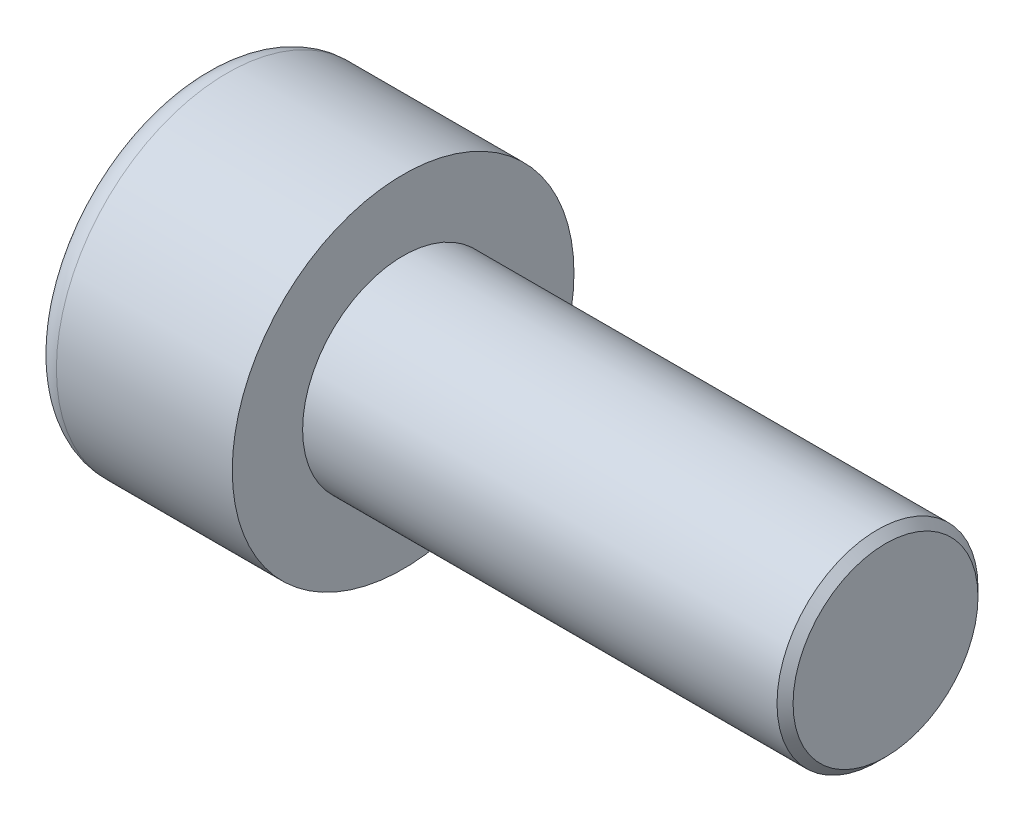
SolidWorks part; units mm, degrees
ref_plane "Front" through (0, 0, 0) normal (0, 0, 1) x (1, 0, 0)
ref_plane "Top" through (0, 0, 0) normal (0, 1, 0) x (1, 0, 0)
ref_plane "Right" through (0, 0, 0) normal (1, 0, 0) x (0, 0, -1)
sketch "Sketch1" plane through (0, 0, 0) normal (1, 0, 0) x (0, 0, -1)
  circle A0 centre (0, 0) radius 4.25
  dimension "dk" = 8.5
extrude "BaseHead" add sketch "Sketch1" along normal blind 5
sketch "Sketch2" plane through (5, 0, 0) normal (1, 0, 0) x (0, 0, -1)
  circle A0 centre (0, 0) radius 2.5
  dimension "d" = 5
extrude "BaseBody" add sketch "Sketch2" along normal blind 12
cosmetic thread "ThreadCosmetic1" parameters "b"=22, "D2"=4.134
sketch "Sketch3" plane through (0, 0, 0) normal (1, 0, 0) x (0, 0, -1)
  line L1 (2.3094, 0) -> (1.1547, 2)
  line L2 (1.1547, 2) -> (-1.1547, 2)
  line L3 (-1.1547, 2) -> (-2.3094, 0)
  line L4 (-2.3094, 0) -> (-1.1547, -2)
  line L5 (-1.1547, -2) -> (1.1547, -2)
  line L6 (1.1547, -2) -> (2.3094, 0)
  circle A0 centre (0, 0) radius 2 construction
  dimension "s" = 4
  dimension "e" = 4.6188
extrude "HexagonSocket" cut sketch "Sketch3" along normal blind 2.5
sketch "Sketch4" plane through (-4.1961, 0.75, 0) normal (0, 0, 1) x (-1, 0, 0)
  line L0 (-6.6961, 2.75) -> (-7.8508, 0.75)
  line L2 (-7.8508, 0.75) -> (-6.6961, 0.75)
  line L3 (-6.6961, 0.75) -> (-6.6961, 2.75)
  line L4 (-5.0351, 0.75) -> (0.839, 0.75) construction
  line L5 (-21.1961, 0.75) -> (-9.1961, 0.75) construction
  line L6 (-9.1961, 0.75) -> (-4.1961, 0.75) construction
  dimension "m" = 60
revolve "Cut-Revolve1" cut sketch "Sketch4" angle 360 about L4
fillet "HeadFillet" [suppressed] radius 0.2
fillet "TopFillet" radius 0.625 1 edges at (0, 0, -4.25)
chamfer "Chamfer1" distance 0.2 angle 45 1 edges at (17, 0, -2.5)
sketch "Sketch5" plane through (0, 0, 0) normal (0, 0, 1) x (1, 0, 0)
  line L0 (16.8, 2.125) -> (17.0165, 2.5)
  line L1 (17.0165, 2.5) -> (17.0165, 2.933)
  line L2 (17.0165, 2.933) -> (16.5835, 2.933)
  line L3 (16.5835, 2.933) -> (16.5835, 2.5)
  line L4 (16.5835, 2.5) -> (16.8, 2.125)
  line L5 (0, 0) -> (7.8886, 0) construction
  line L6 (16.8, -2.5) -> (16.8, 2.5) construction
  dimension "D1" = 5
  dimension "D2" = 0.433
revolve "Cut-Revolve10" [suppressed] cut sketch "Sketch5" angle 360 about L5
pattern_linear "LPattern10" [suppressed] count 42 spacing 0.5196 along (1, 0, 0)
equation "\"r1@TopFillet\" = \"d@Sketch2\" / 8"
equation "\"D1@Chamfer1\" = \"r@HeadFillet\""
equation "\"D1@Sketch5\" = \"d@Sketch2\""
equation "\"D2@Sketch5\" =  ( \"d@Sketch2\" - \"D2@ThreadCosmetic1\" )  / 2"
equation "\"D3@LPattern10\" = \"D2@Sketch5\" * 1.2"
equation "\"D1@LPattern10\" = \"b@ThreadCosmetic1\" / \"D3@LPattern10\""
